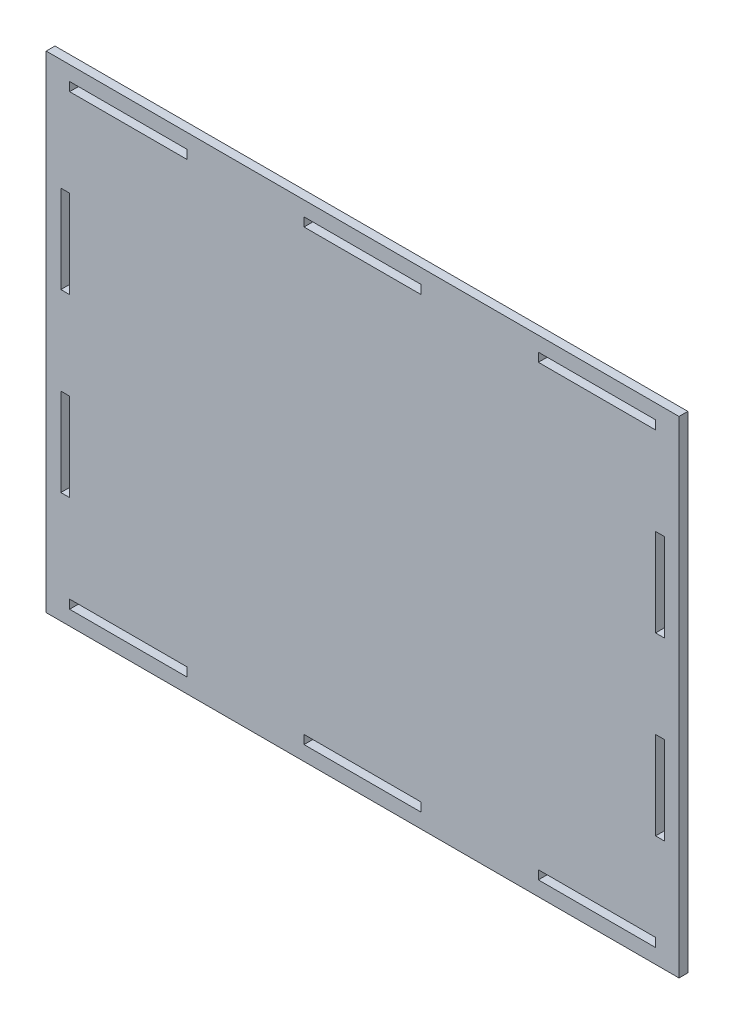
SolidWorks part; units mm, degrees
ref_plane "Front Plane" through (0, 0, 0) normal (0, 0, 1) x (1, 0, 0)
ref_plane "Top Plane" through (0, 0, 0) normal (0, 1, 0) x (1, 0, 0)
ref_plane "Right Plane" through (0, 0, 0) normal (1, 0, 0) x (0, 0, -1)
sketch "Sketch1" plane through (0, 0, 0) normal (0, 0, 1) x (1, 0, 0)
  line L0 (-100, 75) -> (-100, 78)
  line L1 (108, 83) -> (-108, 83)
  line L2 (108, 83) -> (108, -83)
  line L3 (108, -83) -> (-108, -83)
  line L4 (-108, 83) -> (-108, -83)
  line L5 (108, 83) -> (-108, -83) construction
  line L6 (108, -83) -> (-108, 83) construction
  line L7 (100, 75) -> (60, 75)
  line L8 (100, 45) -> (100, 15)
  line L9 (100, -75) -> (60, -75)
  line L10 (-100, 45) -> (-100, 15)
  line L11 (100, 75) -> (-100, -75) construction
  line L12 (100, -75) -> (-100, 75) construction
  line L13 (100, 78) -> (60, 78)
  line L14 (103, 45) -> (103, 15)
  line L15 (100, -78) -> (60, -78)
  line L17 (103, 78) -> (-103, -78) construction
  line L18 (103, -78) -> (-103, 78) construction
  line L19 (-60, 75) -> (-60, 78)
  line L20 (-20, 75) -> (-20, 78)
  line L21 (20, 75) -> (20, 78)
  line L22 (60, 75) -> (60, 78)
  line L23 (100, 75) -> (100, 78)
  line L24 (20, 75) -> (-20, 75)
  line L25 (20, 78) -> (-20, 78)
  line L26 (-60, 75) -> (-100, 75)
  line L27 (-60, 78) -> (-100, 78)
  line L30 (103, -78) -> (-103, 78) construction
  line L31 (100, -75) -> (-100, 75) construction
  line L32 (108, -83) -> (-108, 83) construction
  line L33 (100, -75) -> (100, -78)
  line L34 (60, -75) -> (60, -78)
  line L35 (103, -45) -> (103, -15)
  line L36 (100, -78) -> (60, -78)
  line L37 (100, -75) -> (60, -75)
  line L38 (20, -78) -> (-20, -78)
  line L39 (20, -75) -> (-20, -75)
  line L40 (20, -75) -> (20, -78)
  line L41 (-20, -75) -> (-20, -78)
  line L42 (103, 78) -> (-103, -78) construction
  line L43 (100, 75) -> (-100, -75) construction
  line L44 (108, 83) -> (-108, -83) construction
  line L45 (-60, -78) -> (-100, -78)
  line L46 (-60, -75) -> (-100, -75)
  line L47 (-60, -75) -> (-60, -78)
  line L48 (108, -83) -> (-108, -83)
  line L49 (-100, -75) -> (-100, -78)
  line L50 (-60, -78) -> (-100, -78)
  line L51 (-60, -75) -> (-100, -75)
  line L52 (20, -78) -> (-20, -78)
  line L53 (20, -75) -> (-20, -75)
  line L54 (100, 45) -> (103, 45)
  line L56 (100, 15) -> (103, 15)
  line L57 (100, -15) -> (103, -15)
  line L58 (100, -45) -> (103, -45)
  line L61 (100, -15) -> (100, -45)
  line L62 (103, -15) -> (103, -45)
  line L63 (103, 15) -> (103, 45)
  line L64 (-103, 15) -> (-103, 45)
  line L65 (100, -75) -> (103, -75) [skipped]
  line L66 (-103, -15) -> (-103, -45)
  line L67 (-100, -15) -> (-100, -45)
  line L68 (-100, -45) -> (-103, -45)
  line L69 (-100, -15) -> (-103, -15)
  line L70 (-100, 15) -> (-103, 15)
  line L71 (-100, 45) -> (-103, 45)
  line L72 (-103, -45) -> (-103, -15)
  line L73 (-103, 45) -> (-103, 15)
  line L74 (-100, 45) -> (-100, 15)
  line L75 (-103, 45) -> (-103, 15)
  line L76 (-103, -15) -> (-103, -45)
  line L77 (-100, -15) -> (-100, -45)
  point P0 (0, 0)
  point P6 (0, 0)
  point P11 (0, 0)
  dimension "D1" = 166
  dimension "D2" = 216
  dimension "D3" = 150
  dimension "D4" = 200
  dimension "D5" = 156
  dimension "D6" = 206
  dimension "D7" = 40
  dimension "D9" = 5
  dimension "D8" = 5
extrude "Boss-Extrude1" add sketch "Sketch1" along normal blind 3 contours L1 L4 L3 L2 L71 L10 L70 L64 L69 L67 L68 L66 L61 L57 L35 L58 L56 L8 L54 L14 L49 L46 L47 L45 L41 L39 L40 L38 L34 L9 L33 L15 L27 L19 L26 L0 L25 L21 L24 L20 L23
